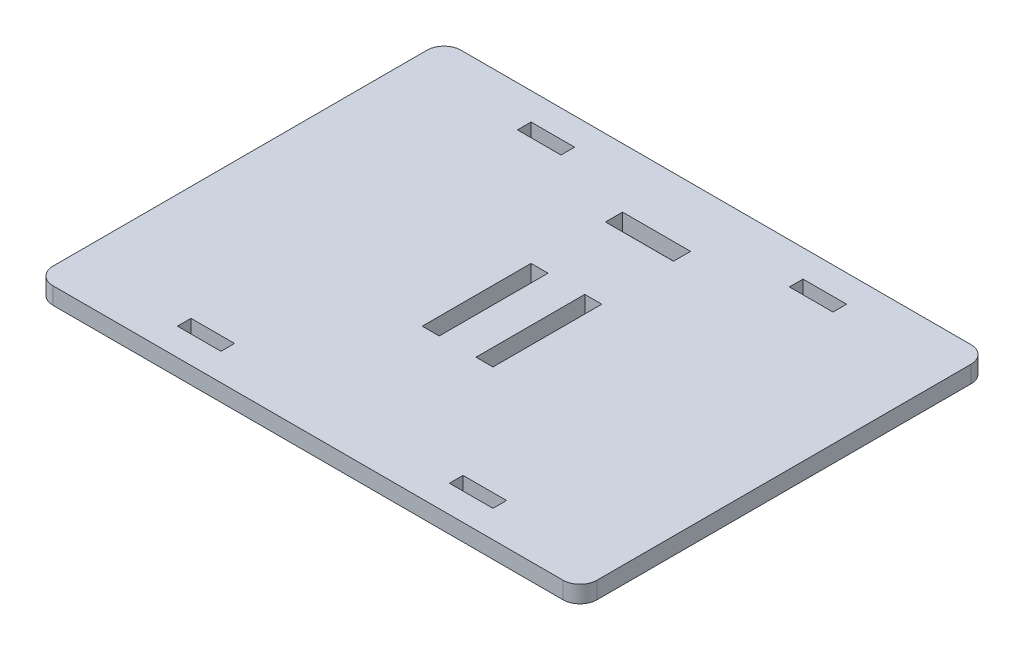
SolidWorks part; units mm, degrees
material "ABS"
ref_plane "Front" through (0, 0, 0) normal (0, 0, 1) x (1, 0, 0)
ref_plane "Top" through (0, 0, 0) normal (0, 1, 0) x (1, 0, 0)
ref_plane "Right" through (0, 0, 0) normal (1, 0, 0) x (0, 0, -1)
sketch "Sketch1" plane through (0, 0, 0) normal (0, 1, 0) x (1, 0, 0)
  line L1 (-50.8, -38.1) -> (50.8, -38.1)
  line L2 (-50.8, -38.1) -> (-50.8, 38.1)
  line L3 (-50.8, 38.1) -> (50.8, 38.1)
  line L4 (50.8, -38.1) -> (50.8, 38.1)
  line L5 (-50.8, -38.1) -> (50.8, 38.1) construction
  line L6 (-50.8, 38.1) -> (50.8, -38.1) construction
  line L11 (-25.4, -31.75) -> (25.4, 31.75) construction
  line L12 (-25.4, 31.75) -> (25.4, -31.75) construction
  line L13 (-29.464, 30.48) -> (-21.336, 30.48)
  line L14 (-29.464, 30.48) -> (-29.464, 33.02)
  line L15 (-29.464, 33.02) -> (-21.336, 33.02)
  line L16 (-21.336, 30.48) -> (-21.336, 33.02)
  line L17 (-29.464, 30.48) -> (-21.336, 33.02) construction
  line L18 (-29.464, 33.02) -> (-21.336, 30.48) construction
  line L19 (-29.464, -33.02) -> (-21.336, -33.02)
  line L20 (-29.464, -33.02) -> (-29.464, -30.48)
  line L21 (-29.464, -30.48) -> (-21.336, -30.48)
  line L22 (-21.336, -33.02) -> (-21.336, -30.48)
  line L23 (-29.464, -33.02) -> (-21.336, -30.48) construction
  line L24 (-29.464, -30.48) -> (-21.336, -33.02) construction
  line L25 (29.464, -33.02) -> (21.336, -33.02)
  line L26 (29.464, -33.02) -> (29.464, -30.48)
  line L27 (29.464, -30.48) -> (21.336, -30.48)
  line L28 (21.336, -33.02) -> (21.336, -30.48)
  line L29 (29.464, -33.02) -> (21.336, -30.48) construction
  line L30 (29.464, -30.48) -> (21.336, -33.02) construction
  line L31 (29.464, 33.02) -> (21.336, 33.02)
  line L32 (29.464, 33.02) -> (29.464, 30.48)
  line L33 (29.464, 30.48) -> (21.336, 30.48)
  line L34 (21.336, 33.02) -> (21.336, 30.48)
  line L35 (29.464, 33.02) -> (21.336, 30.48) construction
  line L36 (29.464, 30.48) -> (21.336, 33.02) construction
  point P0 (0, 0)
  point P6 (0, 0)
  dimension "D1" = 101.6
  dimension "D2" = 76.2
  dimension "D3" = 50.8
  dimension "D4" = 63.5
  dimension "D5" = 8.128
  dimension "D6" = 2.54
  dimension "D7" = 2.54
  dimension "D8" = 8.128
  dimension "D9" = 2.54
  dimension "D10" = 8.128
  dimension "D11" = 8.128
  dimension "D12" = 2.54
extrude "Boss-Extrude1" add sketch "Sketch1" along normal blind 3.175
fillet "Fillet1" radius 3.175 4 edges at (-50.8, 1.5875, -38.1) (50.8, 1.5875, -38.1) (50.8, 1.5875, 38.1) (-50.8, 1.5875, 38.1)
sketch "Sketch2" plane through (0, 3.175, 0) normal (0, 1, 0) x (1, 0, 0)
  line L0 (0, 0) -> (0, 50000) construction
  line L1 (-6.604, -10.16) -> (-3.429, -10.16)
  line L2 (-6.604, -10.16) -> (-6.604, 10.16)
  line L3 (-6.604, 10.16) -> (-3.429, 10.16)
  line L4 (-3.429, -10.16) -> (-3.429, 10.16)
  line L5 (-6.604, -10.16) -> (-3.429, 10.16) construction
  line L6 (-6.604, 10.16) -> (-3.429, -10.16) construction
  line L7 (47.625, 38.1) -> (-47.625, 38.1) construction
  line L8 (6.604, 10.16) -> (3.429, -10.16) construction
  line L9 (6.604, -10.16) -> (3.429, 10.16) construction
  line L10 (3.429, -10.16) -> (3.429, 10.16)
  line L11 (6.604, 10.16) -> (3.429, 10.16)
  line L12 (6.604, -10.16) -> (6.604, 10.16)
  line L13 (6.604, -10.16) -> (3.429, -10.16)
  line L15 (-6.35, 27.0002) -> (6.35, 27.0002)
  line L16 (-6.35, 27.0002) -> (-6.35, 23.7998)
  line L17 (-6.35, 23.7998) -> (6.35, 23.7998)
  line L18 (6.35, 27.0002) -> (6.35, 23.7998)
  line L19 (-6.35, 27.0002) -> (6.35, 23.7998) construction
  line L20 (-6.35, 23.7998) -> (6.35, 27.0002) construction
  point P0 (-5.0165, 0)
  point P10 (0, 38.1)
  point P15 (5.0165, 0)
  point P16 (0, 25.4)
  dimension "D1" = 3.429
  dimension "D2" = 3.175
  dimension "D3" = 20.32
  dimension "D4" = 12.7
  dimension "D5" = 3.2004
  dimension "D6" = 25.4
extrude "Cut-Extrude1" cut sketch "Sketch2" against normal blind 3.175
